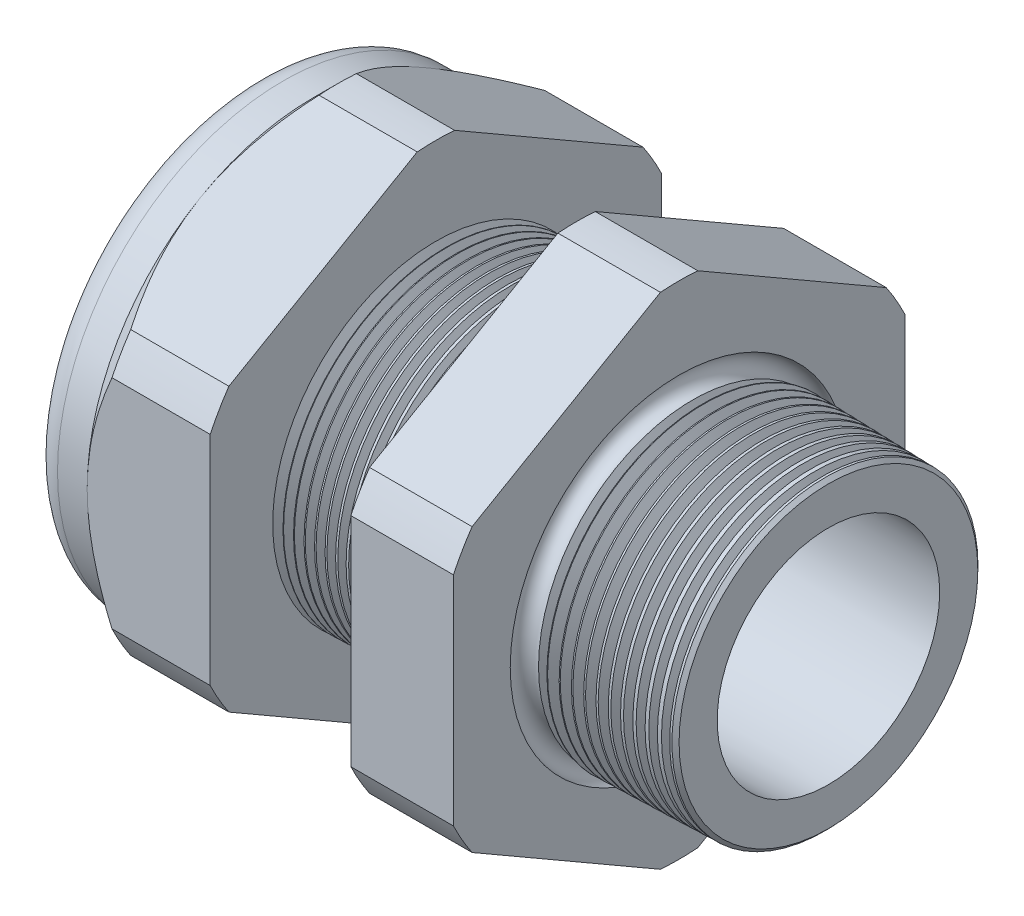
SolidWorks part; units mm, degrees
ref_plane "Front Plane" through (0, 0, 0) normal (0, 0, 1) x (1, 0, 0)
ref_plane "Top Plane" through (0, 0, 0) normal (0, 1, 0) x (1, 0, 0)
ref_plane "Right Plane" through (0, 0, 0) normal (1, 0, 0) x (0, 0, -1)
sketch "Sketch10" plane through (0, 0, 0) normal (0, 0, 1) x (1, 0, 0)
  line L0 (0, 0) -> (-115.3565, 0) construction
  line L1 (-38.862, 9.017) -> (-25.662, 9.017)
  line L2 (3.048, 8.1382) -> (3.048, 11.1862)
  line L3 (-7.874, 11.4722) -> (3.048, 11.1862)
  line L4 (-7.874, 33.02) -> (-7.874, 11.4722)
  line L5 (-7.874, 33.02) -> (-15.374, 33.02)
  line L6 (-15.374, 33.02) -> (-15.374, 11.6686)
  line L7 (-25.662, 11.938) -> (-15.374, 11.6686)
  line L8 (-25.662, 11.938) -> (-25.662, 33.02)
  line L9 (-25.662, 33.02) -> (-34.662, 33.02)
  line L10 (-34.662, 33.02) -> (-34.662, 16.51)
  line L11 (-34.662, 16.51) -> (-38.862, 16.51)
  line L12 (-38.862, 16.51) -> (-38.862, 9.017)
  line L13 (-25.662, 9.017) -> (3.048, 8.1382)
  dimension "D1" = 41.91
  dimension "D2" = 18.034
  dimension "D3" = 1.5
  dimension "D4" = 3.048
  dimension "A" = 23.876
  dimension "D6" = 33.02
  dimension "D8" = 66.04
  dimension "D9" = 4.2
  dimension "D10" = 9
  dimension "D11" = 7.5
  dimension "D" = 10.922
revolve "Revolve2" add sketch "Sketch10" angle 360 about L0
sketch "Sketch12" plane through (-34.662, 0, 0) normal (-1, 0, 0) x (0, 0, 1)
  line L1 (-1.3666, 18.2751) -> (-15.1434, 10.3211)
  line L2 (-16.51, 7.954) -> (-16.51, -7.954)
  line L3 (-15.1434, -10.3211) -> (-1.3666, -18.2751)
  line L4 (1.3666, -18.2751) -> (15.1434, -10.3211)
  line L5 (16.51, -7.954) -> (16.51, 7.954)
  line L6 (15.1434, 10.3211) -> (1.3666, 18.2751)
  circle A0 centre (0, 0) radius 16.51 construction
  arc A1 (1.3666, 18.2751) -> (-1.3666, 18.2751) centre (0, 0) ccw
  arc A2 (-15.1434, 10.3211) -> (-16.51, 7.954) centre (0, 0) ccw
  arc A3 (-16.51, -7.954) -> (-15.1434, -10.3211) centre (0, 0) ccw
  arc A4 (-1.3666, -18.2751) -> (1.3666, -18.2751) centre (0, 0) ccw
  arc A5 (15.1434, -10.3211) -> (16.51, -7.954) centre (0, 0) ccw
  arc A6 (16.51, 7.954) -> (15.1434, 10.3211) centre (0, 0) ccw
  dimension "D2" = 36.6522
  dimension "D1" = 33.02
extrude "Cut-Extrude2" cut sketch "Sketch12" against normal through all flip side to cut
fillet "Fillet4" radius 2.032 1 edges at (-38.862, 0, -16.51)
sketch "Sketch19" plane through (-34.662, 0, 0) normal (-1, 0, 0) x (0, 0, 1)
  line L0 (16.51, 0) -> (16.51, 7.954) construction
  circle A0 centre (0, 0) radius 16.51
extrude "Cut-Extrude3" cut sketch "Sketch19" against normal blind 3.998 draft 45 flip side to cut
chamfer "Chamfer1" distance 0.254 angle 45 1 edges at (3.048, 0, -11.1862)
sketch "Sketch21" plane through (-38.862, 0, 0) normal (-1, 0, 0) x (0, 0, 1)
  circle A0 centre (0, 0) radius 9.017
  circle A2 centre (0, 0) radius 9.017 construction
extrude "plug" add sketch "Sketch21" against normal blind 8.89 separate body
sketch "Sketch22" plane through (-38.862, 0, 0) normal (-1, 0, 0) x (0, 0, 1)
  circle A0 centre (0, 0) radius 8.763
  circle A1 centre (0, 0) radius 9.017 construction
  dimension "D1" = 0.254
extrude "Cut-Extrude4" cut sketch "Sketch22" against normal blind 0.508
sketch "Sketch27" plane through (-38.354, 0, 0) normal (-1, 0, 0) x (0, 0, 1)
  line L0 (-4.3624, 0) -> (4.3624, 0) construction
  circle A0 centre (-5.7028, 0) radius 3.048
  circle A1 centre (0, 0) radius 8.763 construction
  dimension "D1" = 0.0122
  dimension "holedia" = 6.096
extrude "plugholes" cut sketch "Sketch27" against normal through all
pattern_circular "CirPattern1" count 4 over 360 about axis through (0, 0, 0) along (1, 0, 0) of "plugholes"
sketch "Sketch28" [suppressed] plane through (-29.464, 0, 0) normal (-1, 0, 0) x (0, 0, 1)
  circle A0 centre (0, 0) radius 0.762
  dimension "midholedia" = 6.096
extrude "midhole" [suppressed] cut sketch "Sketch28" against normal through all
sketch "Sketch29" plane through (0, 0, 0) normal (0, 0, 1) x (1, 0, 0)
  line L0 (-25.662, 11.938) -> (-24.929, 11.9188)
  line L1 (-15.374, 11.6686) -> (-25.662, 11.938) construction
  line L2 (-24.929, 11.9188) -> (-25.3121, 11.2936)
  line L3 (-25.3121, 11.2936) -> (-25.662, 11.938)
  dimension "D1" = 60
  dimension "D2" = 60
  dimension "D3" = 0.635
revolve "Cut-Revolve1" cut sketch "Sketch29" angle 360 about axis through (0, 0, 0) along (-1, 0, 0)
pattern_linear "LPattern1" count 14 spacing 0.762 along (1, 0, 0) of "Cut-Revolve1"
sketch "Sketch30" plane through (0, 0, 0) normal (0, 0, 1) x (1, 0, 0)
  line L0 (-7.874, 11.4722) -> (-6.9944, 11.4492)
  line L1 (-7.874, 18.2751) -> (-7.874, 10.3211) construction
  line L2 (2.7941, 11.1929) -> (-7.874, 11.4722) construction
  line L3 (-6.9944, 11.4492) -> (-7.4542, 10.6989)
  line L4 (-7.4542, 10.6989) -> (-7.874, 11.4722)
  dimension "D1" = 60
  dimension "D2" = 60
  dimension "D3" = 0.762
revolve "Cut-Revolve2" cut sketch "Sketch30" angle 360 about axis through (0, 0, 0) along (-1, 0, 0)
pattern_linear "LPattern2" count 12 spacing 0.889 along (1, 0, 0) of "Cut-Revolve2"
sketch "Sketch31" [suppressed] plane through (-38.354, 0, 0) normal (-1, 0, 0) x (0, 0, 1)
  line L0 (-1.905, 1.905) -> (1.905, 1.905)
  line L1 (-1.905, -1.905) -> (1.905, -1.905)
  circle A0 centre (0, 0) radius 1.905 construction
  arc A1 (-1.905, 1.905) -> (-1.905, -1.905) centre (-1.905, 0) ccw
  arc A2 (1.905, 1.905) -> (1.905, -1.905) centre (1.905, 0) cw
extrude "Cut-Extrude5" [suppressed] cut sketch "Sketch31" against normal through all
sketch "Sketch32" plane through (0, 0, 0) normal (0, 0, 1) x (1, 0, 0)
  line L0 (-7.874, 18.2751) -> (-7.874, 10.3211) construction
  circle A0 centre (-7.747, 11.4722) radius 0.889
  dimension "D2" = 1.778
  dimension "D1" = 0.127
revolve "Cut-Revolve3" cut sketch "Sketch32" angle 360 about axis through (0, 0, 0) along (-1, 0, 0)
